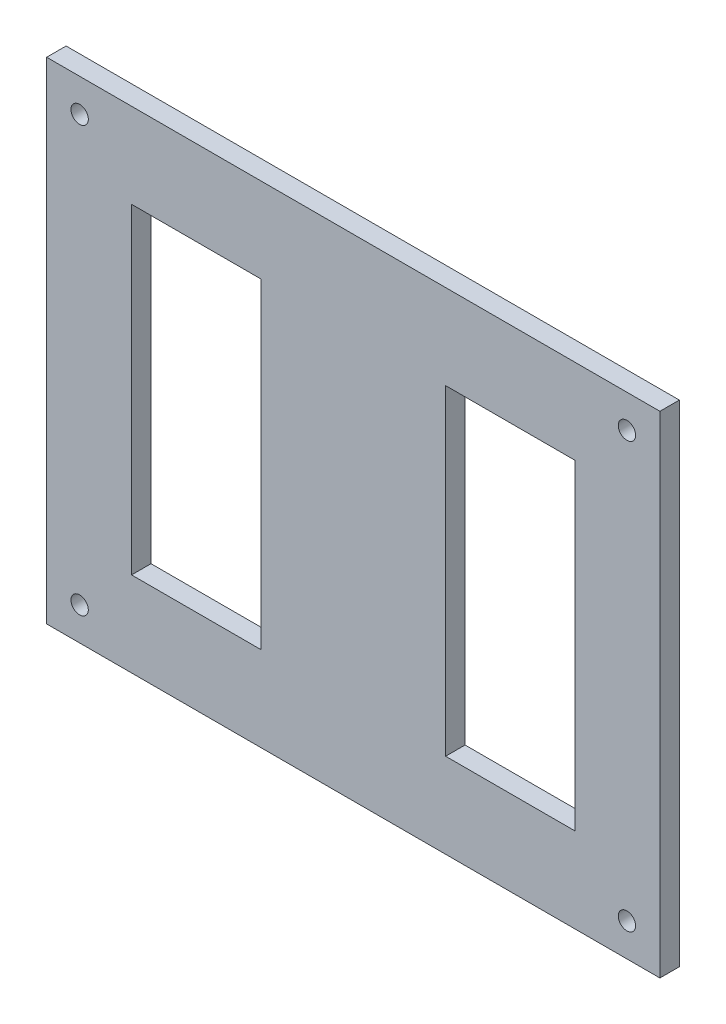
SolidWorks part; units mm, degrees
material "Maple"
ref_plane "Front Plane" through (0, 0, 0) normal (0, 0, 1) x (1, 0, 0)
ref_plane "Top Plane" through (0, 0, 0) normal (0, 1, 0) x (1, 0, 0)
ref_plane "Right Plane" through (0, 0, 0) normal (1, 0, 0) x (0, 0, -1)
sketch "Sketch1" plane through (0, 0, 0) normal (0, 0, 1) x (1, 0, 0)
  line L1 (-50.085, 40.085) -> (50.085, 40.085)
  line L2 (-50.085, 40.085) -> (-50.085, -40.085)
  line L3 (-50.085, -40.085) -> (50.085, -40.085)
  line L4 (50.085, 40.085) -> (50.085, -40.085)
  line L5 (-50.085, 40.085) -> (50.085, -40.085) construction
  line L6 (-50.085, -40.085) -> (50.085, 40.085) construction
  point P0 (0, 0)
  dimension "D1" = 100.17
  dimension "D2" = 80.17
extrude "Boss-Extrude1" add sketch "Sketch1" along normal blind 3.175
sketch "Sketch2" plane through (0, 0, 3.175) normal (0, 0, 1) x (1, 0, 0)
  line L0 (-36.3, 26.3) -> (36.3, 26.3) construction
  line L1 (-37.3, 27.3) -> (37.3, 27.3) construction
  line L2 (-37.3, 27.3) -> (-37.3, -27.3) construction
  line L3 (-37.3, -27.3) -> (37.3, -27.3) construction
  line L4 (37.3, 27.3) -> (37.3, -27.3) construction
  line L5 (-37.3, 27.3) -> (37.3, -27.3) construction
  line L6 (-37.3, -27.3) -> (37.3, 27.3) construction
  line L7 (36.3, 26.3) -> (36.3, -26.3) construction
  line L8 (-36.3, -26.3) -> (36.3, -26.3) construction
  line L9 (-36.3, 26.3) -> (-36.3, -26.3) construction
  line L10 (-30.05, 20.05) -> (30.05, 20.05) construction
  line L11 (30.05, 20.05) -> (30.05, -20.05) construction
  line L12 (-30.05, -20.05) -> (30.05, -20.05) construction
  line L13 (-30.05, 20.05) -> (-30.05, -20.05) construction
  line L14 (-36.3, 0) -> (-15, 0) construction
  line L15 (0, 0) -> (0, 10.2165) construction
  line L16 (-36.3, -26.3) -> (-15, -26.3)
  line L17 (-36.3, -26.3) -> (-36.3, 26.3)
  line L18 (-36.3, 26.3) -> (-15, 26.3)
  line L19 (-15, -26.3) -> (-15, 26.3)
  line L20 (-36.3, -26.3) -> (-15, 26.3) construction
  line L21 (-36.3, 26.3) -> (-15, -26.3) construction
  line L22 (36.3, 26.3) -> (15, 26.3)
  line L23 (15, -26.3) -> (15, 26.3)
  line L24 (36.3, -26.3) -> (15, -26.3)
  line L25 (36.3, -26.3) -> (36.3, 26.3)
  line L26 (-15, 0) -> (0, 0) construction
  line L27 (0, 0) -> (15, 0) construction
  line L28 (36.215, 26.215) -> (15.085, 26.215)
  line L29 (15.085, -26.215) -> (15.085, 26.215)
  line L30 (36.215, -26.215) -> (15.085, -26.215)
  line L31 (36.215, -26.215) -> (36.215, 26.215)
  line L32 (-36.215, 26.215) -> (-15.085, 26.215)
  line L33 (-15.085, -26.215) -> (-15.085, 26.215)
  line L34 (-36.215, -26.215) -> (-15.085, -26.215)
  line L35 (-36.215, -26.215) -> (-36.215, 26.215)
  point P0 (0, 0)
  point P17 (-25.65, 0)
  dimension "D1" = 54.6
  dimension "D2" = 74.6
  dimension "D5" = 21.3
  dimension "D3" = 1
  dimension "D4" = 6.25
  dimension "D6" = 0.085
  dimension "D7" = 0.085
sketch "Sketch3" plane through (0, 0, 3.175) normal (0, 0, 1) x (1, 0, 0)
  line L0 (-44.6967, 34.6967) -> (-50, 40) construction
  line L2 (0, 0) -> (0, 15.7326) construction
  line L3 (0, 0) -> (-6.9587, 0) construction
  line L9 (-50, 40) -> (-50, -40.085)
  line L10 (50.085, 40) -> (-50, 40)
  line L11 (-50, 40) -> (-50, -40.085) construction
  line L12 (50.085, 40) -> (-50, 40) construction
  circle A0 centre (-44.6967, 34.6967) radius 1.415
  circle A1 centre (44.6967, 34.6967) radius 1.415
  circle A2 centre (44.6967, -34.6967) radius 1.415
  circle A3 centre (-44.6967, -34.6967) radius 1.415
  dimension "D3" = 2.83
  dimension "D1" = 45
  dimension "D2" = 7.5
  dimension "D4" = 0.085
extrude "Cut-Extrude2" cut sketch "Sketch3" against normal through all
extrude "Cut-Extrude4" cut sketch "Sketch2" against normal blind 10 contours L28 L29 L30 L31 | L32 L33 L34 L35
equation "\"length\"=100"
equation "\"D1@Sketch1\"=\"length\" + 2*\"kerf\""
equation "\"width\"=80"
equation "\"D2@Sketch1\"=\"width\" + 2*\"kerf\""
equation "\"depth\"=6.35"
equation "\"depth2\"= 6.35 / 2"
equation "\"D1@Boss-Extrude1\"=\"depth2\""
equation "\"D1@Sketch2\"=\"width\"-4*\"depth\""
equation "\"kerf\"= 0.17 / 2"
